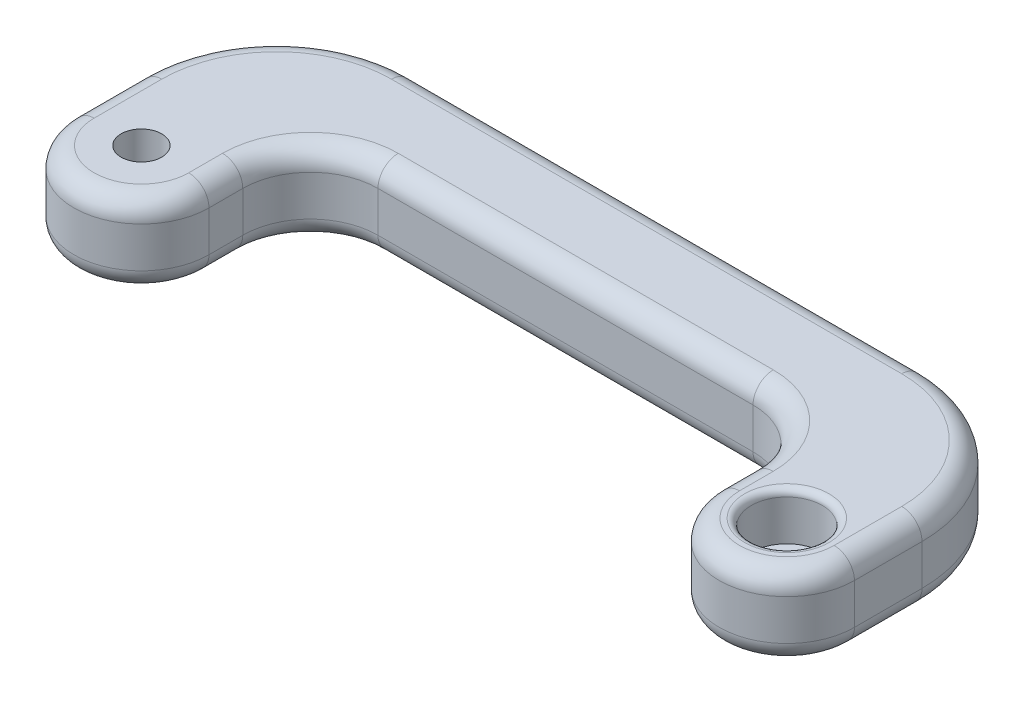
SolidWorks part; units mm, degrees
ref_plane "Front Plane" through (0, 0, 0) normal (0, 0, 1) x (1, 0, 0)
ref_plane "Top Plane" through (0, 0, 0) normal (0, 1, 0) x (1, 0, 0)
ref_plane "Right Plane" through (0, 0, 0) normal (1, 0, 0) x (0, 0, -1)
sketch "Sketch7" plane through (0, 0, 0) normal (0, 1, 0) x (1, 0, 0)
  line L2 (-105.5, 0) -> (-105.5, 30)
  line L3 (-85.5, 0) -> (-85.5, 15)
  line L4 (-105.5, 30) -> (-85.5, 30)
  line L6 (-85.5, 30) -> (10, 30)
  line L7 (-85.5, 15) -> (-10, 15)
  line L10 (10, 0) -> (10, 30.0013)
  line L11 (-10, 0) -> (-10, 15)
  line L12 (10, 30.0013) -> (-10, 30.0013)
  line L13 (-10, 30) -> (-10, 30.0013)
  arc A0 (-10, 0) -> (10, 0) centre (0, 0) ccw
  arc A1 (-105.5, 0) -> (-85.5, 0) centre (-95.5, 0) ccw
  circle A2 centre (-95.5, 0) radius 5
extrude "Boss-Extrude5" add sketch "Sketch7" along normal blind 12 contours L2 A1 L3 L7 L11 A0 L10 L6 L4 A2
sketch "Sketch8" plane through (0, 12, 0) normal (0, 1, 0) x (1, 0, 0)
  circle A0 centre (0, 0) radius 6
fillet "Fillet2" radius 20 2 edges at (10, 6, -30) (-105.5, 6, -30)
fillet "Fillet3" radius 10 2 edges at (-10, 6, -15) (-85.5, 6, -15)
fillet "Fillet5" radius 3 24 edges at (-47.75, 12, -30) (4.1421, 12, -24.1421) (10, 12, -5) (0, 12, 10) (-10, 12, -2.5) (-12.9289, 12, -12.0711) (-47.75, 12, -15) (-82.5711, 12, -12.0711) (-85.5, 12, -2.5) (-95.5, 12, 10) (-105.5, 12, -5) (-105.5, 0, -5) (-95.5, 0, 10) (-85.5, 0, -2.5) (-82.5711, 0, -12.0711) (-47.75, 0, -15) (-12.9289, 0, -12.0711) (-10, 0, -2.5) (0, 0, 10) (10, 0, -5) (4.1421, 0, -24.1421) (-47.75, 0, -30) (-99.6421, 12, -24.1421) (-99.6421, 0, -24.1421)
sketch "Sketch11" plane through (0, 0, 0) normal (0, -1, 0) x (1, 0, 0)
  circle A0 centre (-95.5, 0) radius 5.25
  circle A1 centre (0, 0) radius 5.25
extrude "Cut-Extrude1" cut sketch "Sketch11" against normal blind 25
fillet "Fillet6" radius 1 4 edges at (-95.5, 12, 5.25) (-95.5, 0, -5.25) (0, 12, 5.25) (0, 0, -5.25)
sketch "Sketch12" plane through (0, 12, 0) normal (0, 1, 0) x (1, 0, 0)
  circle A0 centre (0, 0) radius 6.25
  circle A1 centre (0, 0) radius 3
sketch "Sketch13" plane through (0, 0, 0) normal (0, -1, 0) x (1, 0, 0)
  circle A0 centre (0, 0) radius 6.25
  circle A1 centre (0, 0) radius 3
extrude "Boss-Extrude7" add sketch "Sketch13" against normal blind 5
sketch "Sketch14" plane through (0, 12, 0) normal (0, 1, 0) x (1, 0, 0)
  circle A0 centre (-95.5, 0) radius 6.25
  circle A1 centre (-95.5, 0) radius 3
extrude "Boss-Extrude8" add sketch "Sketch14" against normal blind 5
